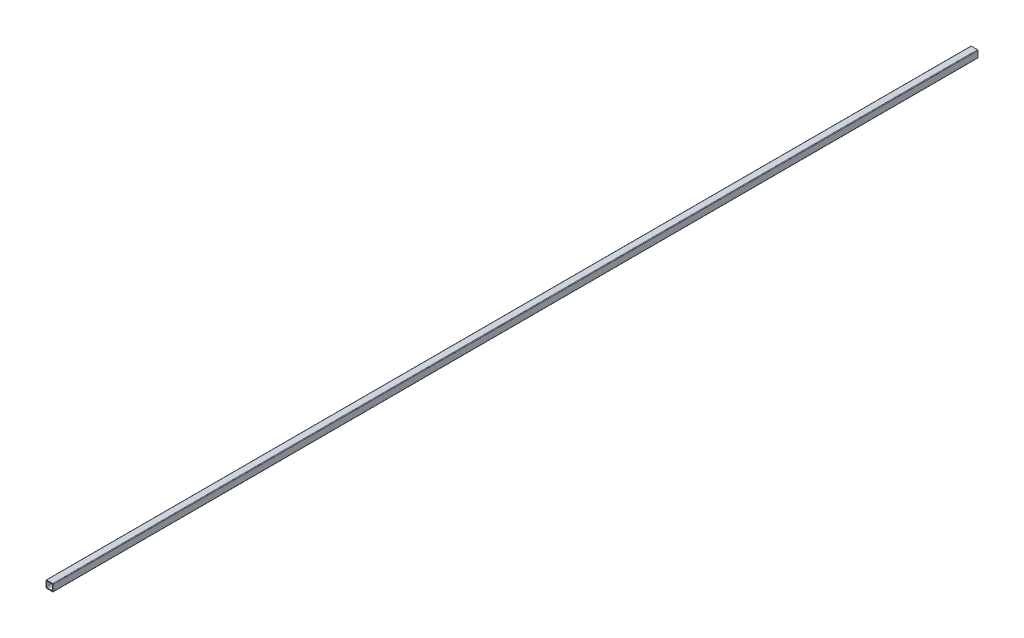
SolidWorks part; units mm, degrees
ref_plane "Front Plane" through (0, 0, 0) normal (0, 0, 1) x (1, 0, 0)
ref_plane "Top Plane" through (0, 0, 0) normal (0, 1, 0) x (1, 0, 0)
ref_plane "Right Plane" through (0, 0, 0) normal (1, 0, 0) x (0, 0, -1)
sketch "Sketch1" plane through (0, 0, 0) normal (0, 0, 1) x (1, 0, 0)
  line L1 (1.524, 0) -> (17.526, 0)
  line L2 (0, 1.524) -> (0, 17.526)
  line L3 (1.524, 19.05) -> (17.526, 19.05)
  line L4 (19.05, 1.524) -> (19.05, 17.526)
  arc A0 (19.05, 17.526) -> (17.526, 19.05) centre (17.526, 17.526) ccw
  arc A1 (19.05, 1.524) -> (17.526, 0) centre (17.526, 1.524) cw
  arc A2 (1.524, 0) -> (0, 1.524) centre (1.524, 1.524) cw
  arc A3 (0, 17.526) -> (1.524, 19.05) centre (1.524, 17.526) cw
  point P7 (19.05, 19.05)
  point P10 (19.05, 0)
  point P13 (0, 0)
  point P16 (0, 19.05)
  dimension "D3" = 1.524
  dimension "D1" = 19.05
  dimension "D2" = 19.05
extrude "Boss-Extrude1" add sketch "Sketch1" against normal blind 2438.4
sketch "Sketch2" plane through (0, 0, 0) normal (0, 0, 1) x (1, 0, 0)
  line L0 (19.05, 1.524) -> (19.05, 17.526) construction
  line L1 (5.08, 17.145) -> (13.97, 17.145)
  line L2 (1.905, 13.97) -> (1.905, 5.08)
  line L3 (5.08, 1.905) -> (13.97, 1.905)
  line L4 (17.145, 13.97) -> (17.145, 5.08)
  line L5 (17.526, 19.05) -> (1.524, 19.05) construction
  line L6 (1.524, 0) -> (17.526, 0) construction
  arc A0 (13.97, 17.145) -> (17.145, 13.97) centre (13.97, 13.97) cw
  arc A1 (17.145, 5.08) -> (13.97, 1.905) centre (13.97, 5.08) cw
  arc A2 (5.08, 1.905) -> (1.905, 5.08) centre (5.08, 5.08) cw
  arc A3 (1.905, 13.97) -> (5.08, 17.145) centre (5.08, 13.97) cw
  point P12 (17.145, 17.145)
  point P15 (17.145, 1.905)
  point P18 (1.905, 1.905)
  dimension "D6" = 3.175
  dimension "D1" = 15.24
  dimension "D2" = 15.24
  dimension "D3" = 1.905
  dimension "D4" = 1.905
  dimension "D5" = 1.905
extrude "Cut-Extrude1" cut sketch "Sketch2" against normal through all
